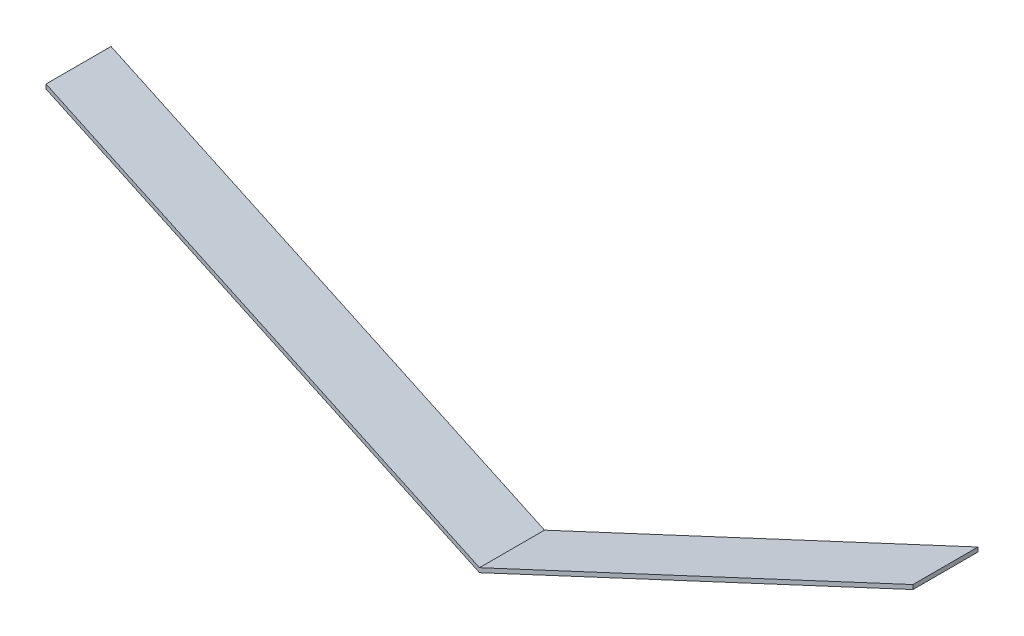
SolidWorks part; units mm, degrees
material "Caoutchouc"
ref_plane "Plan de face" through (0, 0, 0) normal (0, 0, 1) x (1, 0, 0)
ref_plane "Plan de dessus" through (0, 0, 0) normal (0, 1, 0) x (1, 0, 0)
ref_plane "Plan de droite" through (0, 0, 0) normal (1, 0, 0) x (0, 0, -1)
sketch "Esquisse1" plane through (0, 0, 0) normal (0, 0, 1) x (1, 0, 0)
  line L0 (-200, 95.2615) -> (0, 2)
  line L1 (0, 2) -> (200, 95.2615)
  line L3 (-200, 95.2615) -> (-200, 93.2615)
  line L4 (-200, 93.2615) -> (0, 0)
  line L5 (0, 0) -> (200, 93.2615)
  line L6 (200, 93.2615) -> (200, 95.2615)
  dimension "D1" = 130
  dimension "D2" = 400
  dimension "D3" = 2
  dimension "D4" = 65
  dimension "D5" = 2
  dimension "D6" = 65
extrude "Boss.-Extru.1" add sketch "Esquisse1" along normal blind 30 contours L4 L5 L6 L1 L0 L3
